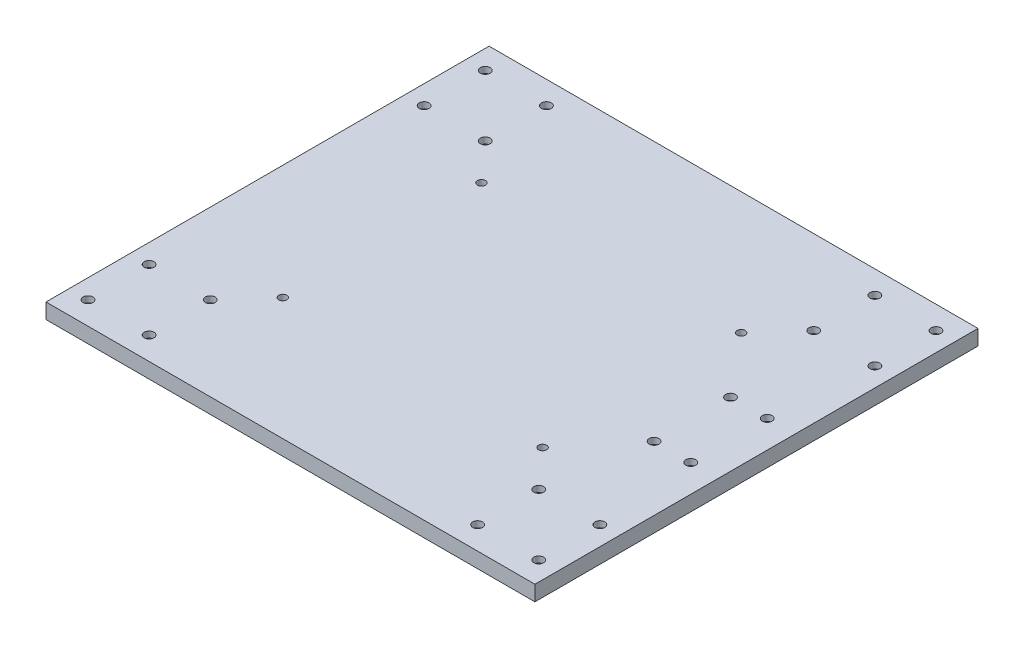
SolidWorks part; units mm, degrees
ref_plane "Спереди" through (0, 0, 0) normal (0, 0, 1) x (1, 0, 0)
ref_plane "Сверху" through (0, 0, 0) normal (0, 1, 0) x (1, 0, 0)
ref_plane "Справа" through (0, 0, 0) normal (1, 0, 0) x (0, 0, -1)
sketch "Эскиз1" plane through (0, 0, 0) normal (0, 1, 0) x (1, 0, 0)
  line L1 (-160, -145) -> (160, -145)
  line L2 (-160, -145) -> (-160, 145)
  line L3 (-160, 145) -> (160, 145)
  line L4 (160, -145) -> (160, 145)
  line L5 (0, -1.8243) -> (0, 39.1997) construction
  line L6 (-107.5, 90) -> (107.5, 90) construction
  line L7 (-85, -65) -> (85, -65) construction
  line L8 (-85, -65) -> (-85, 65) construction
  line L9 (-85, 65) -> (85, 65) construction
  line L10 (85, -65) -> (85, 65) construction
  line L11 (-85, -65) -> (85, 65) construction
  line L12 (-85, 65) -> (85, -65) construction
  line L34 (-130.9839, 130) -> (119.7936, 130) construction
  line L42 (-188.3308, -130) -> (62.4467, -130) construction
  line L43 (-147.5, 101.3194) -> (-147.5, -107.6605) construction
  line L44 (147.5, 107.522) -> (147.5, -74.1306) construction
  line L45 (-107.5, -90) -> (107.5, -90) construction
  line L46 (107.5, -97.0485) -> (107.5, 82.9515) construction
  line L47 (-23.8567, 0) -> (-127.5177, 0) construction
  line L48 (-147.5, 130) -> (-107.5, 130) construction
  line L49 (142, 25) -> (118, 25) construction
  circle A0 centre (-85, 65) radius 2.65
  circle A1 centre (85, 65) radius 2.65
  circle A2 centre (85, -65) radius 2.65
  circle A3 centre (-85, -65) radius 2.65
  circle A4 centre (-147.5, 130) radius 3.2
  circle A5 centre (-147.5, 130) radius 4.5
  circle A6 centre (-107.5, 130) radius 4.5
  circle A7 centre (-107.5, 130) radius 3.2
  circle A8 centre (-107.5, 90) radius 4.5
  circle A9 centre (-107.5, 90) radius 3.2
  circle A10 centre (-147.5, 90) radius 4.5
  circle A11 centre (-147.5, 90) radius 3.2
  circle A12 centre (-147.5, -90) radius 3.2
  circle A13 centre (-147.5, -90) radius 4.5
  circle A14 centre (-107.5, -90) radius 3.2
  circle A15 centre (-107.5, -90) radius 4.5
  circle A16 centre (-107.5, -130) radius 3.2
  circle A17 centre (-107.5, -130) radius 4.5
  circle A18 centre (-147.5, -130) radius 4.5
  circle A19 centre (-147.5, -130) radius 3.2
  circle A20 centre (147.5, -130) radius 3.2
  circle A21 centre (147.5, -130) radius 4.5
  circle A22 centre (107.5, -130) radius 4.5
  circle A23 centre (107.5, -130) radius 3.2
  circle A24 centre (107.5, -90) radius 4.5
  circle A25 centre (107.5, -90) radius 3.2
  circle A26 centre (147.5, -90) radius 4.5
  circle A27 centre (147.5, -90) radius 3.2
  circle A28 centre (147.5, 90) radius 3.2
  circle A29 centre (147.5, 90) radius 4.5
  circle A30 centre (107.5, 90) radius 3.2
  circle A31 centre (107.5, 90) radius 4.5
  circle A32 centre (107.5, 130) radius 3.2
  circle A33 centre (107.5, 130) radius 4.5
  circle A34 centre (147.5, 130) radius 4.5
  circle A35 centre (147.5, 130) radius 3.2
  circle A36 centre (142, 25) radius 3.2
  circle A37 centre (118, 25) radius 3.2
  circle A38 centre (118, -25) radius 3.2
  circle A39 centre (142, -25) radius 3.2
  point P0 (0, 0)
  point P6 (0, 0)
  point P31 (0, 0)
  dimension "D7" = 6.4
  dimension "D15" = 9
  dimension "D2" = 6.4
  dimension "D1" = 320
  dimension "D3" = 170
  dimension "D4" = 130
  dimension "D8" = 12.5
  dimension "D9" = 12.5
  dimension "D11" = 145
  dimension "D12" = 145
  dimension "D13" = 130
  dimension "D6" = 90
  dimension "D10" = 90
  dimension "D14" = 130
  dimension "D18" = 40
  dimension "D19" = 142
  dimension "D21" = 24
  dimension "D22" = 25
  dimension "D16" = 2
  dimension "D17" = 2
  dimension "D20" = 2
extrude "Бобышка-Вытянуть3" add sketch "Эскиз1" along normal blind 10 contours L2 L3 L4 L1 | A19 | A12 | A14 | A16 | A4 | A11 | A7 | A9 | A0 | A3 | A2 | A1 | A32 | A30 | A28 | A25 | A23 | A27 | A20 | A35 | A37 | A38 | A39 | A36
sketch "Эскиз5" plane through (0, 0, 0) normal (0, -1, 0) x (1, 0, 0)
  line L0 (-147.5, 130) -> (-107.5, 130) construction
  line L1 (0, 0) -> (0, 90) construction
  line L2 (41.0364, 0) -> (2.0446, 0) construction
  line L3 (142, 25) -> (118, 25) construction
  circle A0 centre (-147.5, 130) radius 5.25
  circle A1 centre (-107.5, 130) radius 5.25
  circle A2 centre (-107.5, 90) radius 5.25
  circle A3 centre (-147.5, 90) radius 5.25
  circle A4 centre (-147.5, -90) radius 5.25
  circle A5 centre (-107.5, -90) radius 5.25
  circle A6 centre (-107.5, -130) radius 5.25
  circle A7 centre (-147.5, -130) radius 5.25
  circle A8 centre (147.5, -130) radius 5.25
  circle A9 centre (107.5, -130) radius 5.25
  circle A10 centre (107.5, -90) radius 5.25
  circle A11 centre (147.5, -90) radius 5.25
  circle A12 centre (147.5, 90) radius 5.25
  circle A13 centre (107.5, 90) radius 5.25
  circle A14 centre (107.5, 130) radius 5.25
  circle A15 centre (147.5, 130) radius 5.25
  circle A16 centre (142, 25) radius 5.25
  circle A17 centre (118, 25) radius 5.25
  circle A18 centre (118, -25) radius 5.25
  circle A19 centre (142, -25) radius 5.25
  dimension "D9" = 10.5
  dimension "D3" = 40
  dimension "D5" = 25
  dimension "D6" = 142
  dimension "D8" = 24
  dimension "D1" = 2
  dimension "D2" = 2
  dimension "D7" = 2
extrude "Вырез-Вытянуть1" cut sketch "Эскиз5" against normal blind 6
equation "\"D19@Эскиз1\"=160-18"
equation "\"D6@Эскиз5\"=160-18"
